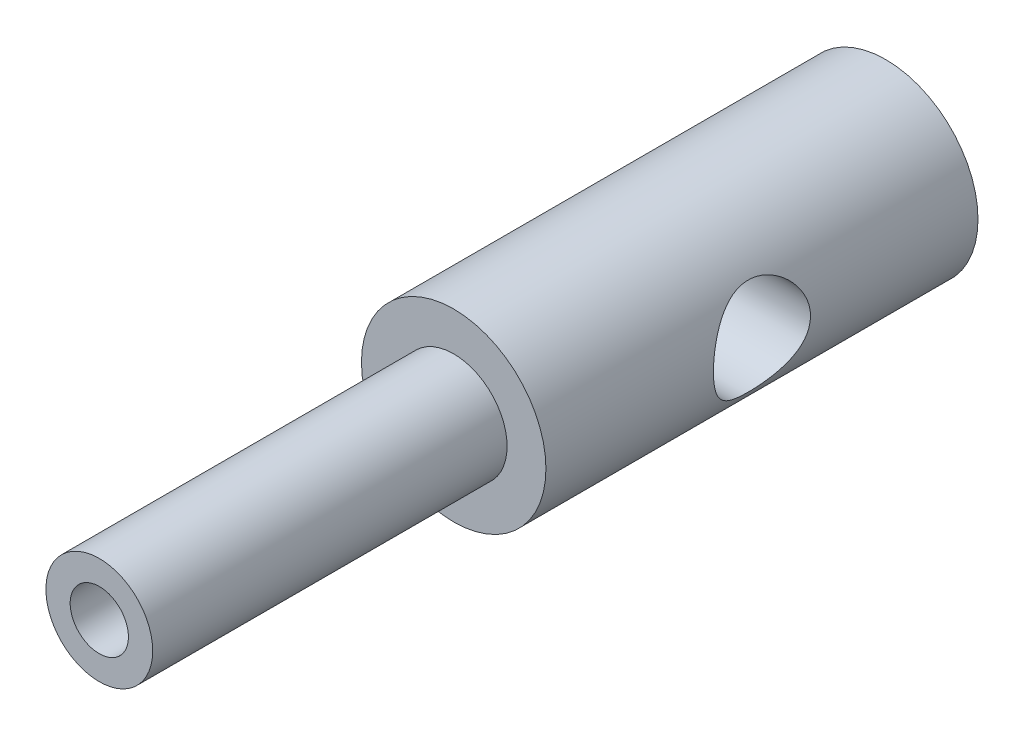
SolidWorks part; units mm, degrees
material "Alloy Steel"
ref_plane "Front Plane" through (0, 0, 0) normal (0, 0, 1) x (1, 0, 0)
ref_plane "Top Plane" through (0, 0, 0) normal (0, 1, 0) x (1, 0, 0)
ref_plane "Right Plane" through (0, 0, 0) normal (1, 0, 0) x (0, 0, -1)
sketch "Sketch1" plane through (0, 0, 0) normal (1, 0, 0) x (0, 0, -1)
  line L0 (-36.6135, 0) -> (28.1064, 0) construction
  line L1 (2.54, 0) -> (11.303, 0)
  line L3 (11.303, 4.826) -> (-11.303, 4.826)
  line L4 (-11.303, 4.826) -> (-11.303, 2.794)
  line L5 (-11.303, 2.794) -> (-29.845, 2.794)
  line L6 (-29.845, 2.794) -> (-29.845, 1.524)
  line L7 (-29.845, 1.524) -> (-11.303, 1.524)
  line L8 (-11.303, 1.524) -> (-11.303, 0)
  line L9 (-11.303, 0) -> (-2.54, 0)
  line L10 (11.303, 0) -> (12.319, 0)
  arc A0 (2.54, 0) -> (-2.54, 0) centre (0, 0) ccw
  arc A1 (11.303, 4.826) -> (12.319, 0) centre (1.3486, 0.2104) cw
  dimension "D1" = 5.08
  dimension "D8" = 10.9724
  dimension "D2" = 4.826
  dimension "D3" = 2.794
  dimension "D4" = 1.524
  dimension "D5" = 11.303
  dimension "D6" = 11.303
  dimension "D7" = 22.606
  dimension "D9" = 1.016
revolve "Revolve1" add sketch "Sketch1" angle 360 about L0
sketch "Sketch2" plane through (0, 0, 0) normal (1, 0, 0) x (0, 0, -1)
  circle A0 centre (0, 0) radius 2.54
  dimension "D1" = 5.08
extrude "Cut-Extrude2" cut sketch "Sketch2" against normal through all and the other way through all
